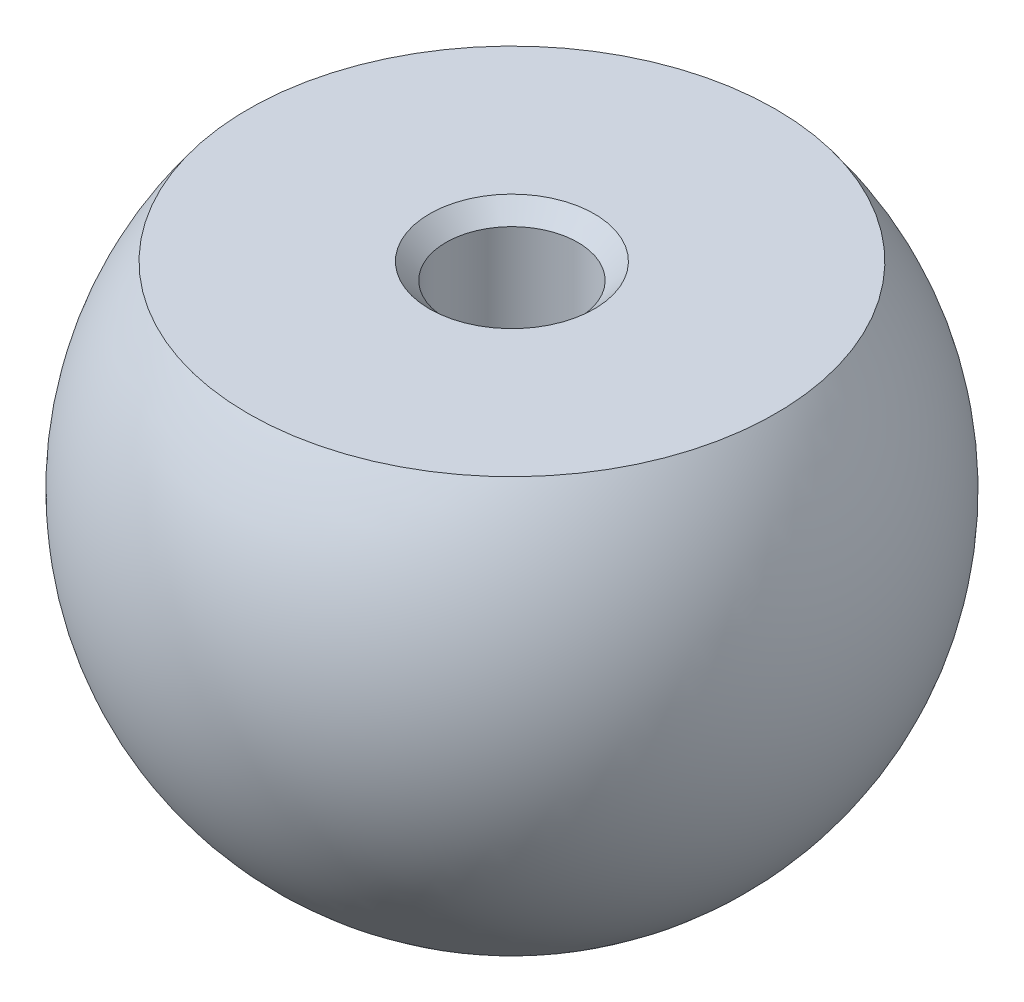
SolidWorks part; units mm, degrees
ref_plane "Front Plane" through (0, 0, 0) normal (0, 0, 1) x (1, 0, 0)
ref_plane "Top Plane" through (0, 0, 0) normal (0, 1, 0) x (1, 0, 0)
ref_plane "Right Plane" through (0, 0, 0) normal (1, 0, 0) x (0, 0, -1)
sketch "Sketch1" plane through (0, 0, 0) normal (1, 0, 0) x (0, 0, -1)
  line L3 (0, 12) -> (16, 12)
  line L4 (0, -20) -> (0, 12)
  arc A0 (0, -20) -> (16, 12) centre (0, 0) ccw
  dimension "D1" = 20
  dimension "D2" = 12
revolve "Revolve2" add sketch "Sketch1" angle 360 about L4
sketch "Sketch2" plane through (0, 12, 0) normal (0, 1, 0) x (1, 0, 0)
  circle A0 centre (0, 0) radius 4
  dimension "D1" = 8
extrude "Cut-Extrude1" cut sketch "Sketch2" against normal blind 20
chamfer "Chamfer1" distance 10 angle 1 1 edges at (0, -8, 4)
chamfer "Chamfer2" distance 1 angle 45 1 edges at (0, 12, 4)
